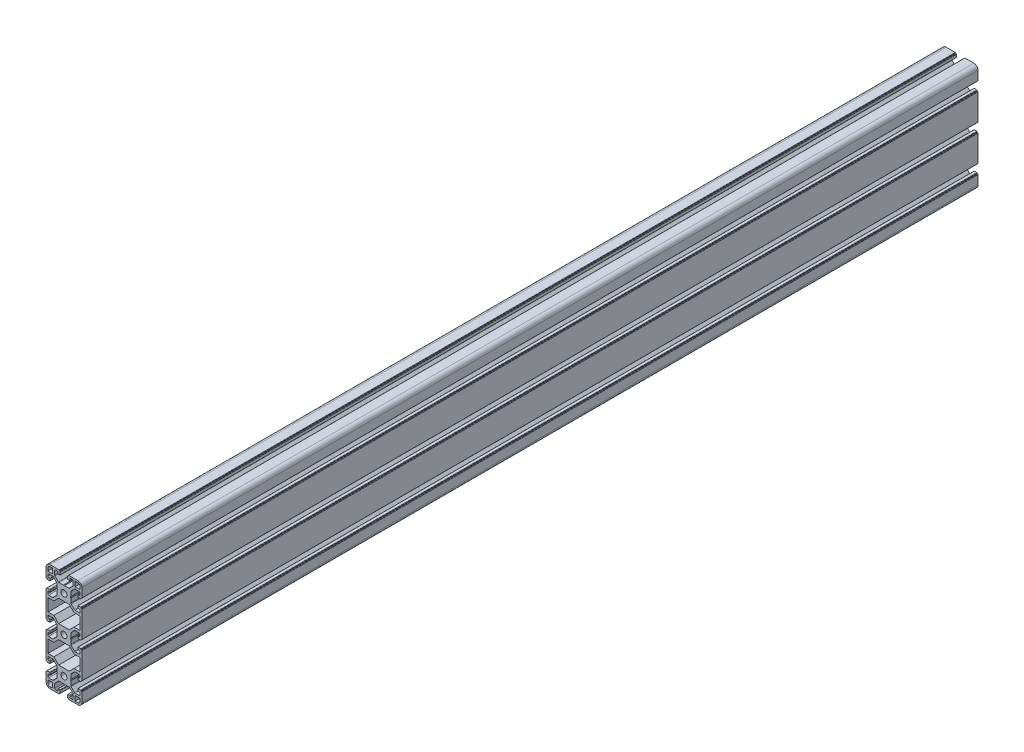
SolidWorks part; units mm, degrees
material "6063 T5"
ref_plane "Спереди" through (0, 0, 0) normal (0, 0, 1) x (1, 0, 0)
ref_plane "Сверху" through (0, 0, 0) normal (0, 1, 0) x (1, 0, 0)
ref_plane "Справа" through (0, 0, 0) normal (1, 0, 0) x (0, 0, -1)
sketch "Эскиз1" plane through (0, 0, 0) normal (0, 0, 1) x (1, 0, 0)
  line L0 (-19.98, 20.5457) -> (20.02, 20.5457) construction
  line L1 (-20, 10.25) -> (-20, 15.5)
  line L2 (-15.5, 20) -> (-10.25, 20)
  line L3 (-35.3695, 20.0843) -> (-35.3695, -99.9157) construction
  line L8 (12.5, 12.5) -> (12.5, 18)
  line L13 (-12.5, 12.5) -> (-18, 12.5)
  line L14 (-12.5, 12.5) -> (-12.5, 18)
  line L19 (-12.5, 18) -> (-15.5, 18)
  line L25 (-18, 12.5) -> (-18, 15.5)
  line L26 (12.5, 18) -> (15.5, 18)
  line L27 (18, 12.5) -> (18, 15.5)
  line L28 (12.5, 12.5) -> (18, 12.5)
  line L29 (15.5, 20) -> (10.25, 20)
  line L30 (20, 10.25) -> (20, 15.5)
  line L31 (0, 0) -> (0, -40) construction
  line L32 (0, -20) -> (-34.3474, -20) construction
  line L33 (-17.8, -27) -> (-17.8, -13)
  line L34 (-17.8, -13) -> (-11.2645, -13)
  line L35 (-11.2645, -13) -> (-5.9645, -7.7)
  line L36 (-5.9645, -7.7) -> (5.9645, -7.7)
  line L37 (11.2645, -13) -> (5.9645, -7.7)
  line L41 (17.8, -13) -> (11.2645, -13)
  line L46 (17.8, -27) -> (17.8, -13)
  line L49 (-17.8, -27) -> (-11.2645, -27)
  line L50 (-11.2645, -27) -> (-5.9645, -32.3)
  line L51 (-20.1159, 24.9491) -> (19.8841, 24.9491) construction
  line L78 (-5.9645, -32.3) -> (5.9645, -32.3)
  line L79 (11.2645, -27) -> (5.9645, -32.3)
  line L84 (17.8, -27) -> (11.2645, -27)
  line L85 (-20, -10.25) -> (-20, -29.75)
  line L86 (-28.8355, 19.0525) -> (-28.8355, -100.9475) construction
  line L87 (-27.3588, -19.7802) -> (-27.3588, -99.7802) construction
  line L88 (20, -10.25) -> (20, -29.75)
  line L89 (20, -50.25) -> (20, -69.75)
  line L90 (-20, -50.25) -> (-20, -69.75)
  line L91 (17.8, -53) -> (11.2645, -53)
  line L92 (11.2645, -53) -> (5.9645, -47.7)
  line L93 (-5.9645, -47.7) -> (5.9645, -47.7)
  line L94 (-11.2645, -53) -> (-5.9645, -47.7)
  line L95 (-17.8, -53) -> (-11.2645, -53)
  line L96 (-17.8, -67) -> (-17.8, -53)
  line L97 (-17.8, -67) -> (-11.2645, -67)
  line L98 (-11.2645, -67) -> (-5.9645, -72.3)
  line L99 (-5.9645, -72.3) -> (5.9645, -72.3)
  line L100 (11.2645, -67) -> (5.9645, -72.3)
  line L101 (17.8, -67) -> (11.2645, -67)
  line L102 (17.8, -67) -> (17.8, -53)
  line L103 (20, -10.25) -> (20, -50.25) construction
  line L104 (12.5, -92.5) -> (18, -92.5)
  line L105 (18, -92.5) -> (18, -95.5)
  line L106 (12.5, -98) -> (15.5, -98)
  line L107 (12.5, -92.5) -> (12.5, -98)
  line L108 (15.5, -100) -> (10.25, -100)
  line L109 (20, -90.25) -> (20, -95.5)
  line L110 (-12.5, -92.5) -> (-18, -92.5)
  line L111 (-18, -92.5) -> (-18, -95.5)
  line L112 (-12.5, -98) -> (-15.5, -98)
  line L113 (-12.5, -92.5) -> (-12.5, -98)
  line L114 (-15.5, -100) -> (-10.25, -100)
  line L115 (-20, -90.25) -> (-20, -95.5)
  arc A0 (-20, 15.5) -> (-15.5, 20) centre (-15.5, 15.5) cw
  arc A6 (-15.5, 18) -> (-18, 15.5) centre (-15.5, 15.5) ccw
  arc A21 (15.5, 18) -> (18, 15.5) centre (15.5, 15.5) cw
  arc A22 (20, 15.5) -> (15.5, 20) centre (15.5, 15.5) ccw
  circle A23 centre (0, 0) radius 3.4
  circle A24 centre (0, -40) radius 3.4
  circle A25 centre (0, -80) radius 3.4
  arc A26 (15.5, -98) -> (18, -95.5) centre (15.5, -95.5) ccw
  arc A27 (20, -95.5) -> (15.5, -100) centre (15.5, -95.5) cw
  arc A28 (-15.5, -98) -> (-18, -95.5) centre (-15.5, -95.5) cw
  arc A29 (-20, -95.5) -> (-15.5, -100) centre (-15.5, -95.5) ccw
  point P4 (0, 0)
  point P38 (0, -7.7)
  point P42 (-17.8, -20)
  point P48 (17.8, -20)
  point P52 (-20, -20)
  point P53 (20, -20)
  line B0 (-20, 10.25) -> (-20, 5.4)
  line B1 (-19.7, 5.1) -> (-19, 5.1)
  line B2 (-19, 5.1) -> (-19, 4.4)
  line B3 (-18.7, 4.1) -> (-15.8, 4.1)
  line B4 (-15.5, 4.4) -> (-15.5, 6.3)
  line B5 (-15.8, 6.6) -> (-17, 6.6)
  line B6 (-18, 7.6) -> (-18, 9.25)
  line B7 (-17, 10.25) -> (-12.4642, 10.25)
  line B8 (-11.7571, 9.9571) -> (-7.9929, 6.1929)
  line B9 (-7.7, 5.4858) -> (-7.7, 0.6)
  line B10 (-7.7, 0) -> (-20, 0) construction
  line B11 (-11.7571, -9.9571) -> (-7.9929, -6.1929)
  line B12 (-17, -10.25) -> (-12.4642, -10.25)
  line B13 (-18, -7.6) -> (-18, -9.25)
  line B14 (-15.8, -6.6) -> (-17, -6.6)
  line B15 (-15.5, -4.4) -> (-15.5, -6.3)
  line B16 (-18.7, -4.1) -> (-15.8, -4.1)
  line B17 (-19, -5.1) -> (-19, -4.4)
  line B18 (-19.7, -5.1) -> (-19, -5.1)
  line B19 (-20, -10.25) -> (-20, -5.4)
  line B20 (-7.7, 0.6) -> (-7.1, 0)
  line B21 (-7.1, 0) -> (-7.7, -0.6)
  line B22 (-7.7, -0.6) -> (-7.7, -5.4858)
  arc B23 (-15.5, 6.3) -> (-15.8, 6.6) centre (-15.8, 6.3) ccw
  arc B24 (-15.8, 4.1) -> (-15.5, 4.4) centre (-15.8, 4.4) ccw
  arc B25 (-19, 4.4) -> (-18.7, 4.1) centre (-18.7, 4.4) ccw
  arc B26 (-20, 5.4) -> (-19.7, 5.1) centre (-19.7, 5.4) ccw
  arc B27 (-7.9929, 6.1929) -> (-7.7, 5.4858) centre (-8.7, 5.4858) cw
  arc B28 (-12.4642, 10.25) -> (-11.7571, 9.9571) centre (-12.4642, 9.25) cw
  arc B29 (-18, 9.25) -> (-17, 10.25) centre (-17, 9.25) cw
  arc B30 (-17, 6.6) -> (-18, 7.6) centre (-17, 7.6) cw
  arc B31 (-17, -6.6) -> (-18, -7.6) centre (-17, -7.6) ccw
  arc B32 (-18, -9.25) -> (-17, -10.25) centre (-17, -9.25) ccw
  arc B33 (-12.4642, -10.25) -> (-11.7571, -9.9571) centre (-12.4642, -9.25) ccw
  arc B34 (-7.9929, -6.1929) -> (-7.7, -5.4858) centre (-8.7, -5.4858) ccw
  arc B35 (-20, -5.4) -> (-19.7, -5.1) centre (-19.7, -5.4) cw
  arc B36 (-19, -4.4) -> (-18.7, -4.1) centre (-18.7, -4.4) cw
  arc B37 (-15.8, -4.1) -> (-15.5, -4.4) centre (-15.8, -4.4) cw
  arc B38 (-15.5, -6.3) -> (-15.8, -6.6) centre (-15.8, -6.3) cw
  line B39 (10.25, 20) -> (5.4, 20)
  line B40 (5.1, 19.7) -> (5.1, 19)
  line B41 (5.1, 19) -> (4.4, 19)
  line B42 (4.1, 18.7) -> (4.1, 15.8)
  line B43 (4.4, 15.5) -> (6.3, 15.5)
  line B44 (6.6, 15.8) -> (6.6, 17)
  line B45 (7.6, 18) -> (9.25, 18)
  line B46 (10.25, 17) -> (10.25, 12.4642)
  line B47 (9.9571, 11.7571) -> (6.1929, 7.9929)
  line B48 (5.4858, 7.7) -> (0.6, 7.7)
  line B49 (0, 7.7) -> (0, 20) construction
  line B50 (-9.9571, 11.7571) -> (-6.1929, 7.9929)
  line B51 (-10.25, 17) -> (-10.25, 12.4642)
  line B52 (-7.6, 18) -> (-9.25, 18)
  line B53 (-6.6, 15.8) -> (-6.6, 17)
  line B54 (-4.4, 15.5) -> (-6.3, 15.5)
  line B55 (-4.1, 18.7) -> (-4.1, 15.8)
  line B56 (-5.1, 19) -> (-4.4, 19)
  line B57 (-5.1, 19.7) -> (-5.1, 19)
  line B58 (-10.25, 20) -> (-5.4, 20)
  line B59 (0.6, 7.7) -> (0, 7.1)
  line B60 (0, 7.1) -> (-0.6, 7.7)
  line B61 (-0.6, 7.7) -> (-5.4858, 7.7)
  arc B62 (6.3, 15.5) -> (6.6, 15.8) centre (6.3, 15.8) ccw
  arc B63 (4.1, 15.8) -> (4.4, 15.5) centre (4.4, 15.8) ccw
  arc B64 (4.4, 19) -> (4.1, 18.7) centre (4.4, 18.7) ccw
  arc B65 (5.4, 20) -> (5.1, 19.7) centre (5.4, 19.7) ccw
  arc B66 (6.1929, 7.9929) -> (5.4858, 7.7) centre (5.4858, 8.7) cw
  arc B67 (10.25, 12.4642) -> (9.9571, 11.7571) centre (9.25, 12.4642) cw
  arc B68 (9.25, 18) -> (10.25, 17) centre (9.25, 17) cw
  arc B69 (6.6, 17) -> (7.6, 18) centre (7.6, 17) cw
  arc B70 (-6.6, 17) -> (-7.6, 18) centre (-7.6, 17) ccw
  arc B71 (-9.25, 18) -> (-10.25, 17) centre (-9.25, 17) ccw
  arc B72 (-10.25, 12.4642) -> (-9.9571, 11.7571) centre (-9.25, 12.4642) ccw
  arc B73 (-6.1929, 7.9929) -> (-5.4858, 7.7) centre (-5.4858, 8.7) ccw
  arc B74 (-5.4, 20) -> (-5.1, 19.7) centre (-5.4, 19.7) cw
  arc B75 (-4.4, 19) -> (-4.1, 18.7) centre (-4.4, 18.7) cw
  arc B76 (-4.1, 15.8) -> (-4.4, 15.5) centre (-4.4, 15.8) cw
  arc B77 (-6.3, 15.5) -> (-6.6, 15.8) centre (-6.3, 15.8) cw
  line B78 (20, -10.25) -> (20, -5.4)
  line B79 (19.7, -5.1) -> (19, -5.1)
  line B80 (19, -5.1) -> (19, -4.4)
  line B81 (18.7, -4.1) -> (15.8, -4.1)
  line B82 (15.5, -4.4) -> (15.5, -6.3)
  line B83 (15.8, -6.6) -> (17, -6.6)
  line B84 (18, -7.6) -> (18, -9.25)
  line B85 (17, -10.25) -> (12.4642, -10.25)
  line B86 (11.7571, -9.9571) -> (7.9929, -6.1929)
  line B87 (7.7, -5.4858) -> (7.7, -0.6)
  line B88 (7.7, 0) -> (20, 0) construction
  line B89 (11.7571, 9.9571) -> (7.9929, 6.1929)
  line B90 (17, 10.25) -> (12.4642, 10.25)
  line B91 (18, 7.6) -> (18, 9.25)
  line B92 (15.8, 6.6) -> (17, 6.6)
  line B93 (15.5, 4.4) -> (15.5, 6.3)
  line B94 (18.7, 4.1) -> (15.8, 4.1)
  line B95 (19, 5.1) -> (19, 4.4)
  line B96 (19.7, 5.1) -> (19, 5.1)
  line B97 (20, 10.25) -> (20, 5.4)
  line B98 (7.7, -0.6) -> (7.1, 0)
  line B99 (7.1, 0) -> (7.7, 0.6)
  line B100 (7.7, 0.6) -> (7.7, 5.4858)
  arc B101 (15.5, -6.3) -> (15.8, -6.6) centre (15.8, -6.3) ccw
  arc B102 (15.8, -4.1) -> (15.5, -4.4) centre (15.8, -4.4) ccw
  arc B103 (19, -4.4) -> (18.7, -4.1) centre (18.7, -4.4) ccw
  arc B104 (20, -5.4) -> (19.7, -5.1) centre (19.7, -5.4) ccw
  arc B105 (7.9929, -6.1929) -> (7.7, -5.4858) centre (8.7, -5.4858) cw
  arc B106 (12.4642, -10.25) -> (11.7571, -9.9571) centre (12.4642, -9.25) cw
  arc B107 (18, -9.25) -> (17, -10.25) centre (17, -9.25) cw
  arc B108 (17, -6.6) -> (18, -7.6) centre (17, -7.6) cw
  arc B109 (17, 6.6) -> (18, 7.6) centre (17, 7.6) ccw
  arc B110 (18, 9.25) -> (17, 10.25) centre (17, 9.25) ccw
  arc B111 (12.4642, 10.25) -> (11.7571, 9.9571) centre (12.4642, 9.25) ccw
  arc B112 (7.9929, 6.1929) -> (7.7, 5.4858) centre (8.7, 5.4858) ccw
  arc B113 (20, 5.4) -> (19.7, 5.1) centre (19.7, 5.4) cw
  arc B114 (19, 4.4) -> (18.7, 4.1) centre (18.7, 4.4) cw
  arc B115 (15.8, 4.1) -> (15.5, 4.4) centre (15.8, 4.4) cw
  arc B116 (15.5, 6.3) -> (15.8, 6.6) centre (15.8, 6.3) cw
  line B117 (20, -50.25) -> (20, -45.4)
  line B118 (19.7, -45.1) -> (19, -45.1)
  line B119 (19, -45.1) -> (19, -44.4)
  line B120 (18.7, -44.1) -> (15.8, -44.1)
  line B121 (15.5, -44.4) -> (15.5, -46.3)
  line B122 (15.8, -46.6) -> (17, -46.6)
  line B123 (18, -47.6) -> (18, -49.25)
  line B124 (17, -50.25) -> (12.4642, -50.25)
  line B125 (11.7571, -49.9571) -> (7.9929, -46.1929)
  line B126 (7.7, -45.4858) -> (7.7, -40.6)
  line B127 (7.7, -40) -> (20, -40) construction
  line B128 (11.7571, -30.0429) -> (7.9929, -33.8071)
  line B129 (17, -29.75) -> (12.4642, -29.75)
  line B130 (18, -32.4) -> (18, -30.75)
  line B131 (15.8, -33.4) -> (17, -33.4)
  line B132 (15.5, -35.6) -> (15.5, -33.7)
  line B133 (18.7, -35.9) -> (15.8, -35.9)
  line B134 (19, -34.9) -> (19, -35.6)
  line B135 (19.7, -34.9) -> (19, -34.9)
  line B136 (20, -29.75) -> (20, -34.6)
  line B137 (7.7, -40.6) -> (7.1, -40)
  line B138 (7.1, -40) -> (7.7, -39.4)
  line B139 (7.7, -39.4) -> (7.7, -34.5142)
  arc B140 (15.5, -46.3) -> (15.8, -46.6) centre (15.8, -46.3) ccw
  arc B141 (15.8, -44.1) -> (15.5, -44.4) centre (15.8, -44.4) ccw
  arc B142 (19, -44.4) -> (18.7, -44.1) centre (18.7, -44.4) ccw
  arc B143 (20, -45.4) -> (19.7, -45.1) centre (19.7, -45.4) ccw
  arc B144 (7.9929, -46.1929) -> (7.7, -45.4858) centre (8.7, -45.4858) cw
  arc B145 (12.4642, -50.25) -> (11.7571, -49.9571) centre (12.4642, -49.25) cw
  arc B146 (18, -49.25) -> (17, -50.25) centre (17, -49.25) cw
  arc B147 (17, -46.6) -> (18, -47.6) centre (17, -47.6) cw
  arc B148 (17, -33.4) -> (18, -32.4) centre (17, -32.4) ccw
  arc B149 (18, -30.75) -> (17, -29.75) centre (17, -30.75) ccw
  arc B150 (12.4642, -29.75) -> (11.7571, -30.0429) centre (12.4642, -30.75) ccw
  arc B151 (7.9929, -33.8071) -> (7.7, -34.5142) centre (8.7, -34.5142) ccw
  arc B152 (20, -34.6) -> (19.7, -34.9) centre (19.7, -34.6) cw
  arc B153 (19, -35.6) -> (18.7, -35.9) centre (18.7, -35.6) cw
  arc B154 (15.8, -35.9) -> (15.5, -35.6) centre (15.8, -35.6) cw
  arc B155 (15.5, -33.7) -> (15.8, -33.4) centre (15.8, -33.7) cw
  line B156 (-20, -29.75) -> (-20, -34.6)
  line B157 (-19.7, -34.9) -> (-19, -34.9)
  line B158 (-19, -34.9) -> (-19, -35.6)
  line B159 (-18.7, -35.9) -> (-15.8, -35.9)
  line B160 (-15.5, -35.6) -> (-15.5, -33.7)
  line B161 (-15.8, -33.4) -> (-17, -33.4)
  line B162 (-18, -32.4) -> (-18, -30.75)
  line B163 (-17, -29.75) -> (-12.4642, -29.75)
  line B164 (-11.7571, -30.0429) -> (-7.9929, -33.8071)
  line B165 (-7.7, -34.5142) -> (-7.7, -39.4)
  line B166 (-7.7, -40) -> (-20, -40) construction
  line B167 (-11.7571, -49.9571) -> (-7.9929, -46.1929)
  line B168 (-17, -50.25) -> (-12.4642, -50.25)
  line B169 (-18, -47.6) -> (-18, -49.25)
  line B170 (-15.8, -46.6) -> (-17, -46.6)
  line B171 (-15.5, -44.4) -> (-15.5, -46.3)
  line B172 (-18.7, -44.1) -> (-15.8, -44.1)
  line B173 (-19, -45.1) -> (-19, -44.4)
  line B174 (-19.7, -45.1) -> (-19, -45.1)
  line B175 (-20, -50.25) -> (-20, -45.4)
  line B176 (-7.7, -39.4) -> (-7.1, -40)
  line B177 (-7.1, -40) -> (-7.7, -40.6)
  line B178 (-7.7, -40.6) -> (-7.7, -45.4858)
  arc B179 (-15.5, -33.7) -> (-15.8, -33.4) centre (-15.8, -33.7) ccw
  arc B180 (-15.8, -35.9) -> (-15.5, -35.6) centre (-15.8, -35.6) ccw
  arc B181 (-19, -35.6) -> (-18.7, -35.9) centre (-18.7, -35.6) ccw
  arc B182 (-20, -34.6) -> (-19.7, -34.9) centre (-19.7, -34.6) ccw
  arc B183 (-7.9929, -33.8071) -> (-7.7, -34.5142) centre (-8.7, -34.5142) cw
  arc B184 (-12.4642, -29.75) -> (-11.7571, -30.0429) centre (-12.4642, -30.75) cw
  arc B185 (-18, -30.75) -> (-17, -29.75) centre (-17, -30.75) cw
  arc B186 (-17, -33.4) -> (-18, -32.4) centre (-17, -32.4) cw
  arc B187 (-17, -46.6) -> (-18, -47.6) centre (-17, -47.6) ccw
  arc B188 (-18, -49.25) -> (-17, -50.25) centre (-17, -49.25) ccw
  arc B189 (-12.4642, -50.25) -> (-11.7571, -49.9571) centre (-12.4642, -49.25) ccw
  arc B190 (-7.9929, -46.1929) -> (-7.7, -45.4858) centre (-8.7, -45.4858) ccw
  arc B191 (-20, -45.4) -> (-19.7, -45.1) centre (-19.7, -45.4) cw
  arc B192 (-19, -44.4) -> (-18.7, -44.1) centre (-18.7, -44.4) cw
  arc B193 (-15.8, -44.1) -> (-15.5, -44.4) centre (-15.8, -44.4) cw
  arc B194 (-15.5, -46.3) -> (-15.8, -46.6) centre (-15.8, -46.3) cw
  line B195 (10.25, -100) -> (5.4, -100)
  line B196 (5.1, -99.7) -> (5.1, -99)
  line B197 (5.1, -99) -> (4.4, -99)
  line B198 (4.1, -98.7) -> (4.1, -95.8)
  line B199 (4.4, -95.5) -> (6.3, -95.5)
  line B200 (6.6, -95.8) -> (6.6, -97)
  line B201 (7.6, -98) -> (9.25, -98)
  line B202 (10.25, -97) -> (10.25, -92.4642)
  line B203 (9.9571, -91.7571) -> (6.1929, -87.9929)
  line B204 (5.4858, -87.7) -> (0.6, -87.7)
  line B205 (0, -87.7) -> (0, -100) construction
  line B206 (-9.9571, -91.7571) -> (-6.1929, -87.9929)
  line B207 (-10.25, -97) -> (-10.25, -92.4642)
  line B208 (-7.6, -98) -> (-9.25, -98)
  line B209 (-6.6, -95.8) -> (-6.6, -97)
  line B210 (-4.4, -95.5) -> (-6.3, -95.5)
  line B211 (-4.1, -98.7) -> (-4.1, -95.8)
  line B212 (-5.1, -99) -> (-4.4, -99)
  line B213 (-5.1, -99.7) -> (-5.1, -99)
  line B214 (-10.25, -100) -> (-5.4, -100)
  line B215 (0.6, -87.7) -> (0, -87.1)
  line B216 (0, -87.1) -> (-0.6, -87.7)
  line B217 (-0.6, -87.7) -> (-5.4858, -87.7)
  arc B218 (6.3, -95.5) -> (6.6, -95.8) centre (6.3, -95.8) cw
  arc B219 (4.1, -95.8) -> (4.4, -95.5) centre (4.4, -95.8) cw
  arc B220 (4.4, -99) -> (4.1, -98.7) centre (4.4, -98.7) cw
  arc B221 (5.4, -100) -> (5.1, -99.7) centre (5.4, -99.7) cw
  arc B222 (6.1929, -87.9929) -> (5.4858, -87.7) centre (5.4858, -88.7) ccw
  arc B223 (10.25, -92.4642) -> (9.9571, -91.7571) centre (9.25, -92.4642) ccw
  arc B224 (9.25, -98) -> (10.25, -97) centre (9.25, -97) ccw
  arc B225 (6.6, -97) -> (7.6, -98) centre (7.6, -97) ccw
  arc B226 (-6.6, -97) -> (-7.6, -98) centre (-7.6, -97) cw
  arc B227 (-9.25, -98) -> (-10.25, -97) centre (-9.25, -97) cw
  arc B228 (-10.25, -92.4642) -> (-9.9571, -91.7571) centre (-9.25, -92.4642) cw
  arc B229 (-6.1929, -87.9929) -> (-5.4858, -87.7) centre (-5.4858, -88.7) cw
  arc B230 (-5.4, -100) -> (-5.1, -99.7) centre (-5.4, -99.7) ccw
  arc B231 (-4.4, -99) -> (-4.1, -98.7) centre (-4.4, -98.7) ccw
  arc B232 (-4.1, -95.8) -> (-4.4, -95.5) centre (-4.4, -95.8) ccw
  arc B233 (-6.3, -95.5) -> (-6.6, -95.8) centre (-6.3, -95.8) ccw
  line B234 (20, -69.75) -> (20, -74.6)
  line B235 (19.7, -74.9) -> (19, -74.9)
  line B236 (19, -74.9) -> (19, -75.6)
  line B237 (18.7, -75.9) -> (15.8, -75.9)
  line B238 (15.5, -75.6) -> (15.5, -73.7)
  line B239 (15.8, -73.4) -> (17, -73.4)
  line B240 (18, -72.4) -> (18, -70.75)
  line B241 (17, -69.75) -> (12.4642, -69.75)
  line B242 (11.7571, -70.0429) -> (7.9929, -73.8071)
  line B243 (7.7, -74.5142) -> (7.7, -79.4)
  line B244 (7.7, -80) -> (20, -80) construction
  line B245 (11.7571, -89.9571) -> (7.9929, -86.1929)
  line B246 (17, -90.25) -> (12.4642, -90.25)
  line B247 (18, -87.6) -> (18, -89.25)
  line B248 (15.8, -86.6) -> (17, -86.6)
  line B249 (15.5, -84.4) -> (15.5, -86.3)
  line B250 (18.7, -84.1) -> (15.8, -84.1)
  line B251 (19, -85.1) -> (19, -84.4)
  line B252 (19.7, -85.1) -> (19, -85.1)
  line B253 (20, -90.25) -> (20, -85.4)
  line B254 (7.7, -79.4) -> (7.1, -80)
  line B255 (7.1, -80) -> (7.7, -80.6)
  line B256 (7.7, -80.6) -> (7.7, -85.4858)
  arc B257 (15.5, -73.7) -> (15.8, -73.4) centre (15.8, -73.7) cw
  arc B258 (15.8, -75.9) -> (15.5, -75.6) centre (15.8, -75.6) cw
  arc B259 (19, -75.6) -> (18.7, -75.9) centre (18.7, -75.6) cw
  arc B260 (20, -74.6) -> (19.7, -74.9) centre (19.7, -74.6) cw
  arc B261 (7.9929, -73.8071) -> (7.7, -74.5142) centre (8.7, -74.5142) ccw
  arc B262 (12.4642, -69.75) -> (11.7571, -70.0429) centre (12.4642, -70.75) ccw
  arc B263 (18, -70.75) -> (17, -69.75) centre (17, -70.75) ccw
  arc B264 (17, -73.4) -> (18, -72.4) centre (17, -72.4) ccw
  arc B265 (17, -86.6) -> (18, -87.6) centre (17, -87.6) cw
  arc B266 (18, -89.25) -> (17, -90.25) centre (17, -89.25) cw
  arc B267 (12.4642, -90.25) -> (11.7571, -89.9571) centre (12.4642, -89.25) cw
  arc B268 (7.9929, -86.1929) -> (7.7, -85.4858) centre (8.7, -85.4858) cw
  arc B269 (20, -85.4) -> (19.7, -85.1) centre (19.7, -85.4) ccw
  arc B270 (19, -84.4) -> (18.7, -84.1) centre (18.7, -84.4) ccw
  arc B271 (15.8, -84.1) -> (15.5, -84.4) centre (15.8, -84.4) ccw
  arc B272 (15.5, -86.3) -> (15.8, -86.6) centre (15.8, -86.3) ccw
  line B273 (-20, -90.25) -> (-20, -85.4)
  line B274 (-19.7, -85.1) -> (-19, -85.1)
  line B275 (-19, -85.1) -> (-19, -84.4)
  line B276 (-18.7, -84.1) -> (-15.8, -84.1)
  line B277 (-15.5, -84.4) -> (-15.5, -86.3)
  line B278 (-15.8, -86.6) -> (-17, -86.6)
  line B279 (-18, -87.6) -> (-18, -89.25)
  line B280 (-17, -90.25) -> (-12.4642, -90.25)
  line B281 (-11.7571, -89.9571) -> (-7.9929, -86.1929)
  line B282 (-7.7, -85.4858) -> (-7.7, -80.6)
  line B283 (-7.7, -80) -> (-20, -80) construction
  line B284 (-11.7571, -70.0429) -> (-7.9929, -73.8071)
  line B285 (-17, -69.75) -> (-12.4642, -69.75)
  line B286 (-18, -72.4) -> (-18, -70.75)
  line B287 (-15.8, -73.4) -> (-17, -73.4)
  line B288 (-15.5, -75.6) -> (-15.5, -73.7)
  line B289 (-18.7, -75.9) -> (-15.8, -75.9)
  line B290 (-19, -74.9) -> (-19, -75.6)
  line B291 (-19.7, -74.9) -> (-19, -74.9)
  line B292 (-20, -69.75) -> (-20, -74.6)
  line B293 (-7.7, -80.6) -> (-7.1, -80)
  line B294 (-7.1, -80) -> (-7.7, -79.4)
  line B295 (-7.7, -79.4) -> (-7.7, -74.5142)
  arc B296 (-15.5, -86.3) -> (-15.8, -86.6) centre (-15.8, -86.3) cw
  arc B297 (-15.8, -84.1) -> (-15.5, -84.4) centre (-15.8, -84.4) cw
  arc B298 (-19, -84.4) -> (-18.7, -84.1) centre (-18.7, -84.4) cw
  arc B299 (-20, -85.4) -> (-19.7, -85.1) centre (-19.7, -85.4) cw
  arc B300 (-7.9929, -86.1929) -> (-7.7, -85.4858) centre (-8.7, -85.4858) ccw
  arc B301 (-12.4642, -90.25) -> (-11.7571, -89.9571) centre (-12.4642, -89.25) ccw
  arc B302 (-18, -89.25) -> (-17, -90.25) centre (-17, -89.25) ccw
  arc B303 (-17, -86.6) -> (-18, -87.6) centre (-17, -87.6) ccw
  arc B304 (-17, -73.4) -> (-18, -72.4) centre (-17, -72.4) cw
  arc B305 (-18, -70.75) -> (-17, -69.75) centre (-17, -70.75) cw
  arc B306 (-12.4642, -69.75) -> (-11.7571, -70.0429) centre (-12.4642, -70.75) cw
  arc B307 (-7.9929, -73.8071) -> (-7.7, -74.5142) centre (-8.7, -74.5142) cw
  arc B308 (-20, -74.6) -> (-19.7, -74.9) centre (-19.7, -74.6) ccw
  arc B309 (-19, -75.6) -> (-18.7, -75.9) centre (-18.7, -75.6) ccw
  arc B310 (-15.8, -75.9) -> (-15.5, -75.6) centre (-15.8, -75.6) ccw
  arc B311 (-15.5, -73.7) -> (-15.8, -73.4) centre (-15.8, -73.7) ccw
  dimension "D12" = 12.3
  dimension "D13" = 2
  dimension "D2" = 3
  dimension "D3" = 120
  dimension "D5" = 2.5
  dimension "D6" = 5.5
  dimension "D4" = 4.5
  dimension "D8" = 6.8
  dimension "D1" = 20
  dimension "D7" = 40
  dimension "D9" = 2.5
  dimension "D10" = 2.2
  dimension "D11" = 7
  dimension "D14" = 40
  dimension "D15" = 120
  dimension "D16" = 40
sketch_block_instance "8B(20,5PL_cut)-1"
sketch_block "8B(20,5PL_cut)" parameters "D7"=0.3, "D8"=1, "D12"=0.3, "D1"=12.3, "D2"=4.5, "D3"=8.2, "D4"=20.5, "D5"=10.2, "D6"=135, "D9"=1, "D10"=2.5, "D11"=2.5, "D13"=1.2
sketch_block_instance "8B(20,5PL_cut)-4"
sketch_block_instance "8B(20,5PL_cut)-5"
sketch_block_instance "8B(20,5PL_cut)-6"
sketch_block_instance "8B(20,5PL_cut)-7"
sketch_block_instance "8B(20,5PL_cut)-8"
sketch_block_instance "8B(20,5PL_cut)-9"
sketch_block_instance "8B(20,5PL_cut)-10"
extrude "Бобышка-Вытянуть1" add sketch "Эскиз1" along normal blind 1000 contours B288 B311 B287 B304 B286 B305 B285 B306 B284 B307 B295 B294 B293 B282 B300 B281 B301 B280 B302 B279 B303 B278 B296 B277 B297 B276 B298 B275 B274 B299 B273 L115 A29 L114 B214 B230 B213 B212 B231 B211 B232 B210 B233 B209 B226 B208 B227 B207 B228 B206 B229
